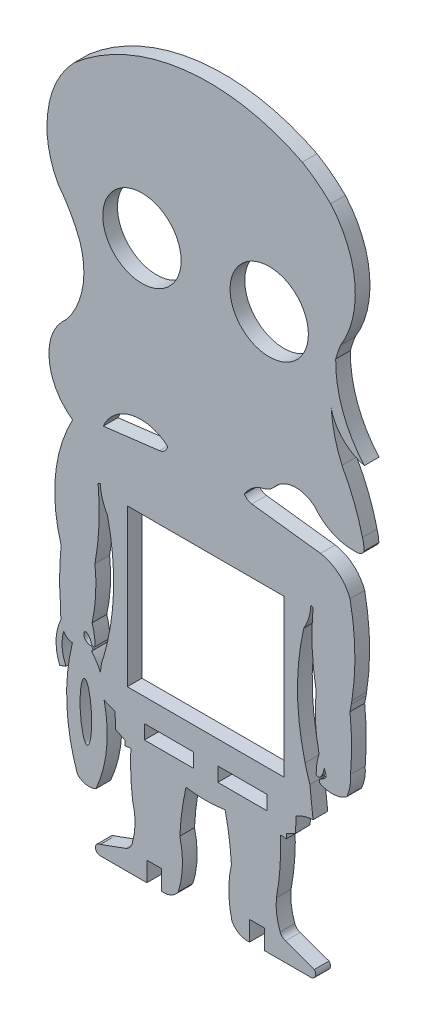
SolidWorks part; units mm, degrees
ref_plane "Alzado" through (0, 0, 0) normal (0, 0, 1) x (1, 0, 0)
ref_plane "Planta" through (0, 0, 0) normal (0, 1, 0) x (1, 0, 0)
ref_plane "Vista lateral" through (0, 0, 0) normal (1, 0, 0) x (0, 0, -1)
sketch "Model" plane through (0, 0, 0) normal (0, 0, 1) x (1, 0, 0)
  line L0 (17.2154, -13.508) -> (18.4854, -13.0144)
  line L1 (26.2734, -15.0983) -> (28.4966, -16.009)
  line L2 (28.4966, -16.009) -> (28.6465, -19.1471)
  line L3 (28.6465, -19.1471) -> (30.503, -20.047)
  line L4 (30.503, -20.047) -> (30.5032, -21.047)
  line L5 (30.5032, -21.047) -> (31.7287, -20.9209)
  line L6 (30.6653, -39.1317) -> (25.4632, -41.0405)
  line L7 (25.5064, -43.0478) -> (35.0051, -43.0464)
  line L8 (35.0051, -43.0464) -> (35.0045, -39.0464)
  line L9 (35.0045, -39.0464) -> (38.0003, -39.0459)
  line L10 (38.0003, -39.0459) -> (38.0051, -43.045)
  line L11 (56.0003, -43.0446) -> (56.0003, -39.0446)
  line L12 (56.0003, -39.0446) -> (59.0003, -39.0446)
  line L13 (59.0003, -39.0446) -> (59.0003, -43.0446)
  line L14 (59.0003, -43.0446) -> (68.5374, -43.0442)
  line L15 (69.2206, -41.2894) -> (63.3213, -39.1687)
  line L16 (62.2735, -20.9186) -> (63.4991, -21.0446)
  line L17 (63.4991, -21.0446) -> (63.4991, -20.0446)
  line L18 (63.4991, -20.0446) -> (65.3555, -19.1444)
  line L19 (65.3555, -19.1444) -> (65.5049, -16.0063)
  line L20 (68.9525, -14.9454) -> (68.3057, -9.0041)
  line L21 (68.5056, 22.7821) -> (68.9567, 22.6035)
  line L22 (26.0958, 33.2739) -> (37.5604, 34.6781)
  line L23 (59.5003, -15.1446) -> (49.5003, -15.1446)
  line L24 (49.5003, -15.1446) -> (49.5003, -18.0446)
  line L25 (49.5003, -18.0446) -> (59.5003, -18.0446)
  line L26 (59.5003, -18.0446) -> (59.5003, -15.1446)
  line L27 (76.7776, 9.4331) -> (76.8921, 10.1237)
  line L28 (70.4991, 32.9554) -> (56.4403, 34.6778)
  line L29 (71.2095, -4.5904) -> (71.5751, -5.5724)
  line L30 (34.5003, -18.0446) -> (44.5003, -18.0446)
  line L31 (44.5003, -18.0446) -> (44.5003, -15.1446)
  line L32 (44.5003, -15.1446) -> (34.5003, -15.1446)
  line L33 (34.5003, -15.1446) -> (34.5003, -18.0446)
  line L34 (47.5003, 21.6334) -> (63.0003, 21.6334)
  line L35 (63.0003, 21.6334) -> (63.0003, -10.3666)
  line L36 (63.0003, -10.3666) -> (31.0003, -10.3666)
  line L37 (31.0003, -10.3666) -> (31.0003, 21.6334)
  line L38 (31.0003, 21.6334) -> (47.5003, 21.6334)
  line L39 (25.0435, 22.6043) -> (25.491, 22.7814)
  line L40 (25.5261, -10.5658) -> (25.7227, -8.9203)
  circle A0 centre (34.0003, 70.4774) radius 8
  circle A1 centre (60.0003, 70.4774) radius 8
  arc A2 (79.3928, 37.8023) -> (79.0422, 40.0346) centre (71.5069, 37.7073) ccw
  arc A3 (76.7743, -0.5499) -> (76.778, 4.1356) centre (19.0303, 1.839) ccw
  arc A4 (23.6313, -6.2905) -> (24.231, -6.7324) centre (24.1202, -6.2549) ccw
  arc A5 (23.6313, -6.2905) -> (22.7819, -4.9801) centre (21.6228, -6.6618) ccw
  arc A6 (22.7819, -4.9801) -> (22.1267, -5.3441) centre (22.5393, -5.315) ccw
  arc A7 (22.1267, -5.3441) -> (23.5828, -6.8486) centre (23.535, -5.4381) ccw
  arc A8 (23.6866, -7.7019) -> (23.5828, -6.8486) centre (23.5319, -7.2878) ccw
  arc A9 (25.5261, -10.5658) -> (23.6866, -7.7019) centre (14.3817, -15.7011) ccw
  arc A10 (73.5796, 68.882) -> (79.4324, 52.9545) centre (97.1582, 68.5071) ccw
  arc A11 (74.5518, 71.7822) -> (73.5796, 68.882) centre (100.0574, 61.6197) ccw
  arc A12 (74.5518, 71.7822) -> (72.5437, 95.8466) centre (57.2894, 82.4577) ccw
  arc A13 (72.5437, 95.8466) -> (66.7529, 100.3127) centre (51.8127, 74.9538) ccw
  arc A14 (79.0422, 40.0346) -> (74.8617, 50.7115) centre (38.2727, 30.2283) ccw
  arc A15 (72.6648, 59.7596) -> (74.8617, 50.7115) centre (100.0574, 61.6197) ccw
  arc A16 (72.6648, 59.7596) -> (79.4324, 52.9545) centre (81.5656, 61.8435) ccw
  arc A17 (66.7529, 100.3127) -> (20.188, 94.6259) centre (47.6957, 62.872) ccw
  arc A18 (20.188, 94.6259) -> (14.7564, 82.9958) centre (34.0347, 81.0757) ccw
  arc A19 (14.7564, 82.9958) -> (16.8295, 71.5665) centre (33.6146, 80.5138) ccw
  arc A20 (21.3016, 63.6479) -> (16.8295, 71.5665) centre (-7.6917, 52.496) ccw
  arc A21 (18.4842, 48.2756) -> (21.3016, 63.6479) centre (5.9816, 58.5113) ccw
  arc A22 (18.4842, 48.2756) -> (15.0468, 41.5067) centre (24.7293, 40.8469) ccw
  arc A23 (15.0468, 41.5067) -> (19.8375, 31.253) centre (26.4099, 40.5698) ccw
  arc A24 (19.8375, 31.253) -> (17.4945, 7.8987) centre (46.763, 16.7571) ccw
  arc A25 (17.4945, 7.8987) -> (17.3871, -3.1389) centre (75.1393, 1.8186) ccw
  arc A26 (17.3871, -3.1389) -> (17.4865, -5.2069) centre (26.3033, -3.7469) ccw
  arc A27 (17.4865, -5.2069) -> (17.2154, -13.508) centre (26.5799, -9.6589) ccw
  arc A28 (18.0049, -7.0682) -> (18.4854, -13.0144) centre (26.3108, -9.3896) ccw
  arc A29 (18.0049, -7.0682) -> (19.7994, -8.1952) centre (19.9919, -5.8967) ccw
  arc A30 (19.7994, -8.1952) -> (20.8037, -30.9196) centre (58.6729, -17.8616) ccw
  arc A31 (20.8037, -30.9196) -> (24.6049, -31.621) centre (23.1902, -28.6369) ccw
  arc A32 (24.6049, -31.621) -> (26.2734, -15.0983) centre (0.6458, -20.8561) ccw
  arc A33 (31.7287, -20.9209) -> (32.0837, -29.9769) centre (85.8236, -23.3353) ccw
  arc A34 (32.1207, -37.0668) -> (32.0837, -29.9769) centre (19.3409, -33.5884) ccw
  arc A35 (30.6653, -39.1317) -> (32.1207, -37.0668) centre (29.7293, -36.9267) ccw
  arc A36 (25.4632, -41.0405) -> (25.5064, -43.0478) centre (25.4963, -42.0439) ccw
  arc A37 (38.0051, -43.045) -> (41.42, -41.459) centre (38.4659, -39.5677) ccw
  arc A38 (41.42, -41.459) -> (41.7399, -31.4345) centre (23.7596, -35.8782) ccw
  arc A39 (42.9975, -22.154) -> (41.7399, -31.4345) centre (95.1478, -33.9464) ccw
  arc A40 (42.9975, -22.154) -> (51.0049, -22.1534) centre (46.9994, 2.9767) ccw
  arc A41 (52.2783, -31.1863) -> (51.0049, -22.1534) centre (-5.9201, -34.7843) ccw
  arc A42 (52.2783, -31.1863) -> (52.3894, -41.1457) centre (73.1724, -35.9336) ccw
  arc A43 (52.3894, -41.1457) -> (56.0003, -43.0446) centre (55.5744, -39.4719) ccw
  arc A44 (68.5374, -43.0442) -> (69.2206, -41.2894) centre (68.4686, -42.0071) ccw
  arc A45 (62.2344, -38.1279) -> (63.3213, -39.1687) centre (63.7024, -37.6827) ccw
  arc A46 (61.471, -32.4648) -> (62.2344, -38.1279) centre (73.8692, -33.6766) ccw
  arc A47 (61.471, -32.4648) -> (62.2735, -20.9186) centre (12.2602, -23.2433) ccw
  arc A48 (68.9525, -14.9454) -> (65.5049, -16.0063) centre (69.1732, -21.7949) ccw
  arc A49 (67.3326, -5.6815) -> (68.3057, -9.0041) centre (115.3489, 6.5775) ccw
  arc A50 (67.0645, 18.0226) -> (67.3326, -5.6815) centre (115.9322, 6.7216) ccw
  arc A51 (67.0645, 18.0226) -> (68.5056, 22.7821) centre (58.5053, 23.212) ccw
  arc A52 (37.5604, 34.6781) -> (39.2732, 36.246) centre (37.3172, 36.6633) ccw
  arc A53 (39.2732, 36.246) -> (26.0958, 33.2739) centre (33.77, 29.9474) ccw
  arc A54 (76.778, 4.1356) -> (76.4991, 7.9554) centre (19.0303, 1.839) ccw
  arc A55 (76.4991, 7.9554) -> (76.7776, 9.4331) centre (27.4991, 17.9554) ccw
  arc A56 (76.8921, 10.1237) -> (76.4991, 27.9554) centre (27.4991, 17.9554) ccw
  arc A57 (76.4991, 27.9554) -> (70.4991, 32.9554) centre (69.1241, 25.2054) ccw
  arc A58 (54.9343, 35.6932) -> (56.4403, 34.6778) centre (56.6835, 36.6629) ccw
  arc A59 (58.2263, 38.4363) -> (54.9343, 35.6932) centre (60.4184, 32.4585) ccw
  arc A60 (58.7626, 38.5914) -> (58.2263, 38.4363) centre (59.6035, 34.6808) ccw
  arc A61 (58.7626, 38.5914) -> (61.0249, 39.978) centre (57.9217, 42.502) ccw
  arc A62 (69.3616, 40.5721) -> (61.0249, 39.978) centre (65.4722, 36.3607) ccw
  arc A63 (69.3616, 40.5721) -> (77.4095, 36.8496) centre (77.0168, 46.5614) ccw
  arc A64 (77.868, 36.8506) -> (77.4095, 36.8496) centre (77.6519, 30.8545) ccw
  arc A65 (77.868, 36.8506) -> (79.3928, 37.8023) centre (77.9259, 38.4554) ccw
  arc A66 (69.2355, 24.9932) -> (69.6002, 8.066) centre (121.7414, 17.657) ccw
  arc A67 (69.6002, 8.066) -> (70.1802, -2.665) centre (102.5324, 4.4649) ccw
  arc A68 (70.1802, -2.665) -> (69.5948, -6.6103) centre (81.2681, -6.3263) ccw
  arc A69 (69.5948, -6.6103) -> (70.387, -6.6923) centre (70.0414, -6.1638) ccw
  arc A70 (70.387, -6.6923) -> (71.2095, -4.5904) centre (67.6138, -4.3953) ccw
  arc A71 (71.1918, -6.5411) -> (71.5751, -5.5724) centre (70.8067, -5.8285) ccw
  arc A72 (71.1918, -6.5411) -> (70.3629, -7.1042) centre (73.5461, -10.8977) ccw
  arc A73 (70.3629, -7.1042) -> (70.4385, -7.8325) centre (70.7266, -7.4346) ccw
  arc A74 (70.4385, -7.8325) -> (75.591, -7.618) centre (72.8138, -2.8981) ccw
  arc A75 (75.591, -7.618) -> (75.9333, -7.2182) centre (75.1802, -6.9199) ccw
  arc A76 (75.9333, -7.2182) -> (76.6107, -3.118) centre (67.6648, -3.7461) ccw
  arc A77 (76.6107, -3.118) -> (76.7743, -0.5499) centre (19.0303, 1.839) ccw
  arc A78 (24.231, -6.7324) -> (24.3988, -6.6151) centre (23.9606, -6.167) ccw
  arc A79 (24.3988, -6.6151) -> (23.8191, -2.6642) centre (12.9878, -6.2714) ccw
  arc A80 (23.8191, -2.6642) -> (24.3995, 8.0667) centre (-8.3273, 4.4557) ccw
  arc A81 (24.3995, 8.0667) -> (25.0435, 22.6043) centre (-27.5158, 17.6495) ccw
  arc A82 (25.491, 22.7814) -> (26.9451, 17.9817) centre (35.5906, 23.2211) ccw
  arc A83 (25.7227, -8.9203) -> (26.956, -4.5019) centre (-22.3899, 6.8901) ccw
  arc A84 (26.956, -4.5019) -> (26.9451, 17.9817) centre (-21.9018, 6.7163) ccw
  ellipse E0 centre (22.5481, -19.0504) end of major axis (22.2981, -13.2884) minor radius 1.1575
extrude "Saliente-Extruir1" add sketch "Model" along normal blind 3 contours A76 A77 A3 A54 A55 L27 A56 A57 L28 A58 A59 A60 A61 A62 A63 A64 A65 A2 A14 A15 A16 A10 A11 A12 A13 A17 A18 A19 A20 A21 A22 A23 A24 A25 A26 A27 L0 A28 A29 A30 A31 A32 L1 L2 L3 L4 L5 A33 A34 A35 L6
